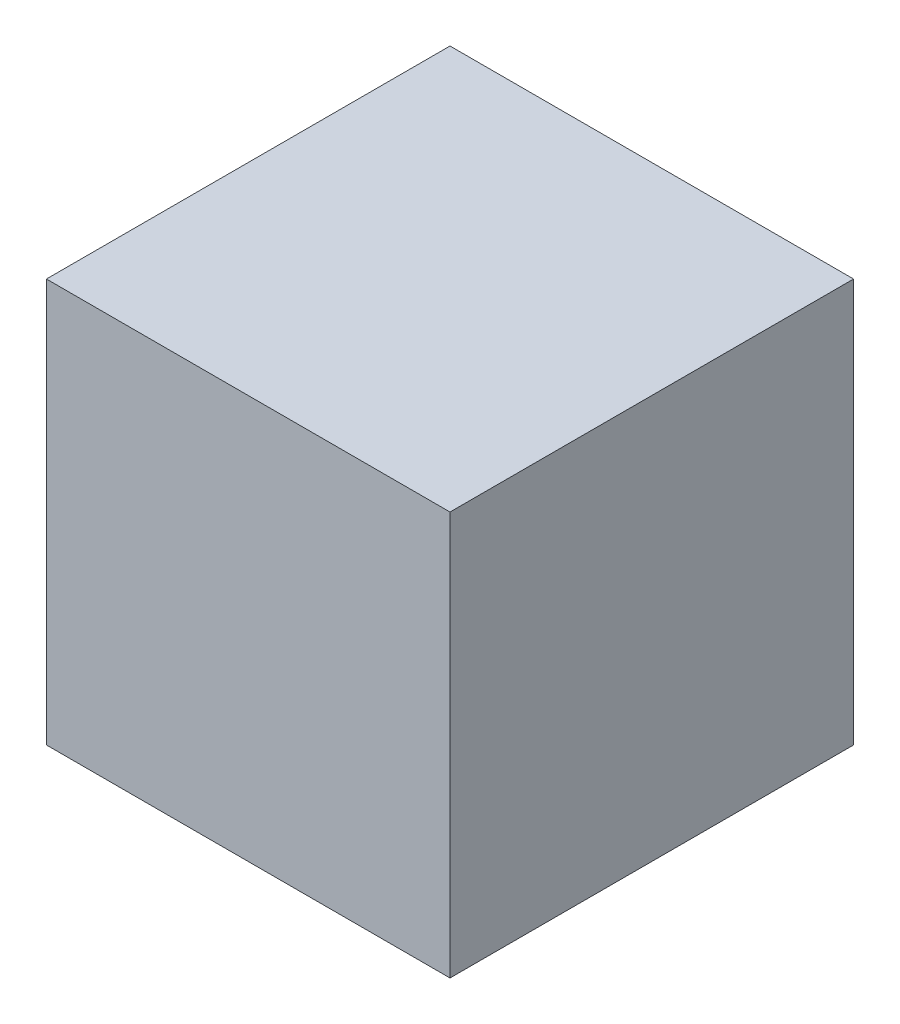
SolidWorks part; units mm, degrees
ref_plane "Přední rovina" through (0, 0, 0) normal (0, 0, 1) x (1, 0, 0)
ref_plane "Horní rovina" through (0, 0, 0) normal (0, 1, 0) x (1, 0, 0)
ref_plane "Pravá rovina" through (0, 0, 0) normal (1, 0, 0) x (0, 0, -1)
sketch "Sketch1" plane through (0, 0, 0) normal (0, 0, 1) x (1, 0, 0)
  line L1 (0, 0) -> (60, 0)
  line L2 (0, 0) -> (0, 60)
  line L3 (0, 60) -> (60, 60)
  line L4 (60, 0) -> (60, 60)
  dimension "D1" = 60
  dimension "D2" = 60
extrude "Boss-Extrude1" add sketch "Sketch1" along normal blind 60
